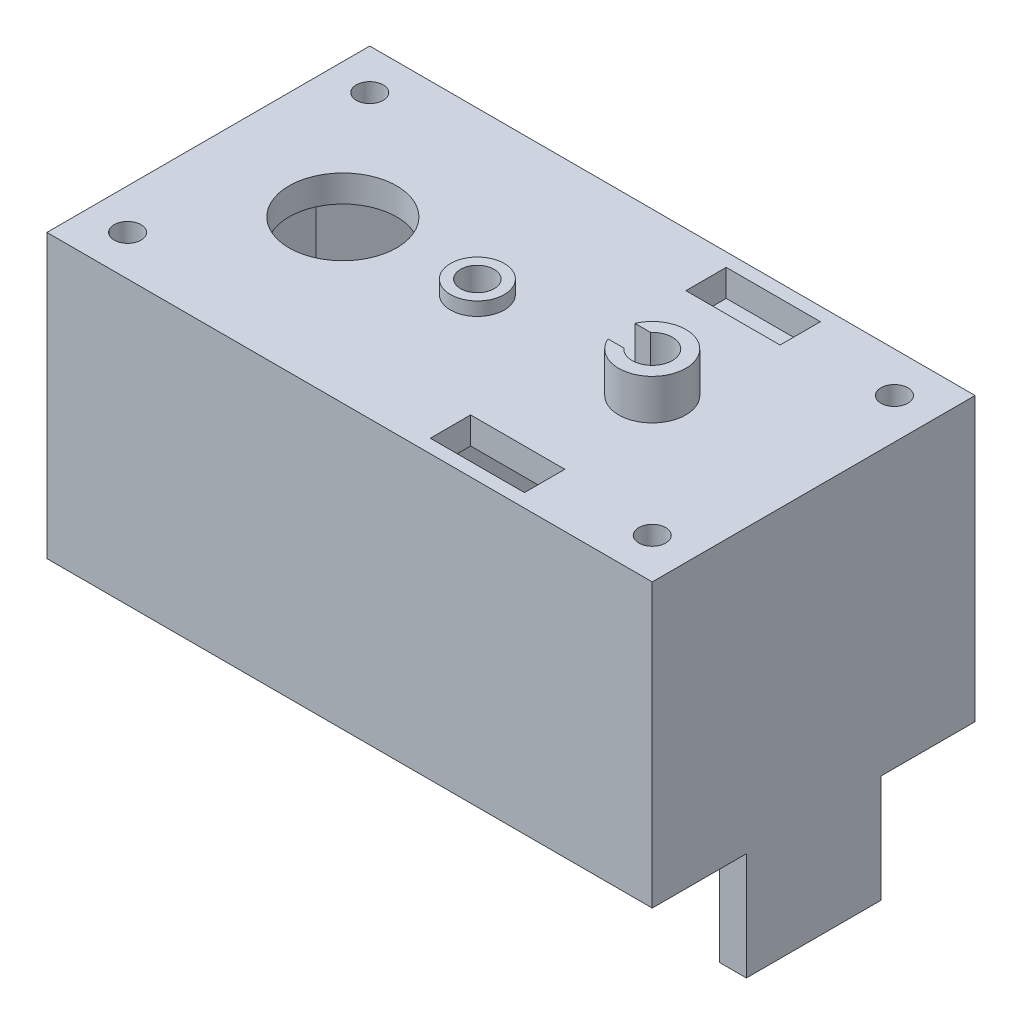
SolidWorks part; units mm, degrees
ref_plane "Front Plane" through (0, 0, 0) normal (0, 0, 1) x (1, 0, 0)
ref_plane "Top Plane" through (0, 0, 0) normal (0, 1, 0) x (1, 0, 0)
ref_plane "Right Plane" through (0, 0, 0) normal (1, 0, 0) x (0, 0, -1)
sketch "Sketch1" plane through (0, 0, 0) normal (0, 1, 0) x (1, 0, 0)
  line L0 (10.25, -5) -> (10.25, 5)
  line L1 (11.25, -6) -> (-11.25, -6)
  line L2 (11.25, -6) -> (11.25, 6)
  line L3 (11.25, 6) -> (-11.25, 6)
  line L4 (-11.25, -6) -> (-11.25, 6)
  line L5 (11.25, -6) -> (-11.25, 6) construction
  line L6 (11.25, 6) -> (-11.25, -6) construction
  line L7 (10.25, 5) -> (-1.25, 5)
  line L8 (-10.25, -5) -> (-10.25, 5)
  line L9 (10.25, -5) -> (-1.25, -5)
  line L10 (-2.25, 5) -> (-2.25, -5)
  line L11 (-1.25, 5) -> (-1.25, -5)
  line L12 (-2.25, 5) -> (-10.25, 5)
  line L13 (-2.25, -5) -> (-10.25, -5)
  line L14 (10.25, 5) -> (-10.25, 5) construction
  line L16 (10.25, -5) -> (-10.25, -5) construction
  point P0 (0, 0)
  dimension "D1" = 22.5
  dimension "D2" = 12
  dimension "D4" = 1
  dimension "D5" = 9
  dimension "D3" = 1
extrude "Boss-Extrude1" add sketch "Sketch1" along normal blind 10.5
sketch "Sketch2" plane through (0, 10.5, 0) normal (0, 1, 0) x (1, 0, 0)
  line L0 (0, 0) -> (-5.437, 0) construction
  line L1 (11.25, -6) -> (-11.25, -6)
  line L2 (11.25, -6) -> (11.25, 6)
  line L3 (11.25, 6) -> (-11.25, 6)
  line L4 (-11.25, -6) -> (-11.25, 6)
  line L5 (11.25, -6) -> (-11.25, 6) construction
  line L6 (11.25, 6) -> (-11.25, -6) construction
  line L7 (6, 0) -> (6, -2.943) construction
  line L8 (2.5, 5.5) -> (6, 5.5)
  line L9 (2.5, 5.5) -> (2.5, 4)
  line L10 (2.5, 4) -> (6, 4)
  line L11 (6, 5.5) -> (6, 4)
  line L12 (10.25, 5) -> (-1.25, 5) construction
  line L13 (2.5, -4) -> (6, -4)
  line L14 (6, -5.5) -> (6, -4)
  line L15 (2.5, -5.5) -> (6, -5.5)
  line L16 (2.5, -5.5) -> (2.5, -4)
  circle A0 centre (-6.25, 0) radius 2
  circle A1 centre (5.25, 0) radius 0.75
  point P0 (0, 0)
  dimension "D1" = 4
  dimension "D3" = 1.5
  dimension "D2" = 5
  dimension "D4" = 6
  dimension "D5" = 1.5
  dimension "D6" = 3.5
  dimension "D7" = 0.5
extrude "Boss-Extrude2" add sketch "Sketch2" against normal blind 1
sketch "Sketch3" plane through (0, 10.5, 0) normal (0, 1, 0) x (1, 0, 0)
  line L1 (2.5, 5.5) -> (6, 5.5)
  line L2 (2.5, 5.5) -> (2.5, 4)
  line L3 (2.5, 4) -> (6, 4)
  line L4 (6, 5.5) -> (6, 4)
  line L5 (2.5, -4) -> (6, -4)
  line L6 (2.5, -4) -> (2.5, -5.5)
  line L7 (2.5, -5.5) -> (6, -5.5)
  line L8 (6, -4) -> (6, -5.5)
extrude "Cut-Extrude1" cut sketch "Sketch3" against normal blind 1
sketch "Sketch4" plane through (-2.25, 0, 0) normal (-1, 0, 0) x (0, 0, 1)
  line L0 (6, 10.5) -> (6, 0) construction
  line L1 (-5, 0) -> (5, 0)
  line L2 (-5, 0) -> (-5, 2.5)
  line L3 (-5, 2.5) -> (5, 2.5)
  line L4 (5, 0) -> (5, 2.5)
  dimension "D1" = 2.5
  dimension "D2" = 1
extrude "Cut-Extrude2" cut sketch "Sketch4" against normal blind 1
chamfer "Chamfer1" distance 2 angle 45 4 edges at (10.25, 4.75, -5) (10.25, 4.75, 5) (-10.25, 4.75, 5) (-10.25, 4.75, -5)
sketch "Sketch5" plane through (0, 0, 0) normal (0, -1, 0) x (1, 0, 0)
  line L0 (-8.25, 5) -> (-12.0322, 5) construction
  line L1 (-10.25, 3) -> (-10.25, 6.7253) construction
  line L2 (-10.25, -3) -> (-10.25, 3) construction
  line L3 (-8.25, 5) -> (-10.25, 3) construction
  line L4 (-0.6537, 0) -> (3.7515, 0) construction
  line L5 (0, 2.1669) -> (0, -1.9374) construction
  circle A0 centre (-9.75, 4.5) radius 0.5
  circle A4 centre (9.75, 4.5) radius 0.5
  circle A5 centre (9.75, -4.5) radius 0.5
  circle A6 centre (-9.75, -4.5) radius 0.5
  dimension "D1" = 1
extrude "Cut-Extrude3" cut sketch "Sketch5" against normal through all
sketch "Sketch6" plane through (0, 0, 0) normal (0, -1, 0) x (1, 0, 0)
  line L0 (10.25, 3) -> (10.25, -3) construction
  line L1 (10.25, 2.5) -> (11.25, 2.5)
  line L2 (10.25, 2.5) -> (10.25, -2.5)
  line L3 (10.25, -2.5) -> (11.25, -2.5)
  line L4 (11.25, 2.5) -> (11.25, -2.5)
  line L5 (11.25, 6) -> (11.25, -6) construction
  line L6 (6.1934, 0) -> (12.7177, 0) construction
  point P11 (10.25, 0)
  dimension "D1" = 5
extrude "Boss-Extrude3" add sketch "Sketch6" along normal blind 4
sketch "Sketch7" plane through (0, 10.5, 0) normal (0, 1, 0) x (1, 0, 0)
  line L0 (-1.25, -5) -> (-1.25, 5) construction
  line L1 (-1.25, -5) -> (-1.25, 5) construction
  circle A0 centre (-1.25, 0) radius 0.625
  circle A1 centre (-1.25, 0) radius 1
  dimension "D1" = 1.25
  dimension "D2" = 2
extrude "Boss-Extrude4" add sketch "Sketch7" against normal blind 1.75 contours L1 A1 A0
sketch "Sketch8" plane through (0, 10.5, 0) normal (0, 1, 0) x (1, 0, 0)
  circle A0 centre (-1.25, 0) radius 0.625 construction
  circle A1 centre (-1.25, 0) radius 0.625
extrude "Cut-Extrude4" cut sketch "Sketch8" against normal blind 1.75
sketch "Sketch9" plane through (0, 8.75, 0) normal (0, -1, 0) x (1, 0, 0)
  circle A0 centre (-1.25, 0) radius 1 construction
  circle A1 centre (-1.25, 0) radius 1
extrude "Boss-Extrude5" add sketch "Sketch9" along normal blind 0.25
sketch "Sketch10" plane through (0, 10.5, 0) normal (0, 1, 0) x (1, 0, 0)
  circle A0 centre (-1.25, 0) radius 0.625 construction
  circle A1 centre (-1.25, 0) radius 1 construction
  circle A2 centre (-1.25, 0) radius 0.625
  circle A3 centre (-1.25, 0) radius 1
extrude "Boss-Extrude6" add sketch "Sketch10" along normal blind 0.5
sketch "Sketch11" plane through (0, 10.5, 0) normal (0, 1, 0) x (1, 0, 0)
  circle A0 centre (5.25, 0) radius 0.75 construction
  circle A1 centre (5.25, 0) radius 0.75
  circle A2 centre (5.25, 0) radius 1.25
  dimension "D1" = 0.5
extrude "Boss-Extrude7" add sketch "Sketch11" along normal blind 1.5
sketch "Sketch12" plane through (0, 12, 0) normal (0, 1, 0) x (1, 0, 0)
  line L0 (4.1044, 0.5) -> (4.691, 0.5)
  line L1 (4.1044, -0.5) -> (4.691, -0.5)
  line L2 (3.2751, 0) -> (5.6329, 0) construction
  circle A0 centre (5.25, 0) radius 1.25 construction
  circle A1 centre (5.25, 0) radius 0.75 construction
  arc A2 (4.1044, 0.5) -> (4.1044, -0.5) centre (5.25, 0) ccw
  arc A3 (4.691, 0.5) -> (4.691, -0.5) centre (5.25, 0) ccw
  dimension "D1" = 0.5
  dimension "D2" = 1
extrude "Cut-Extrude5" cut sketch "Sketch12" against normal blind 1.5
